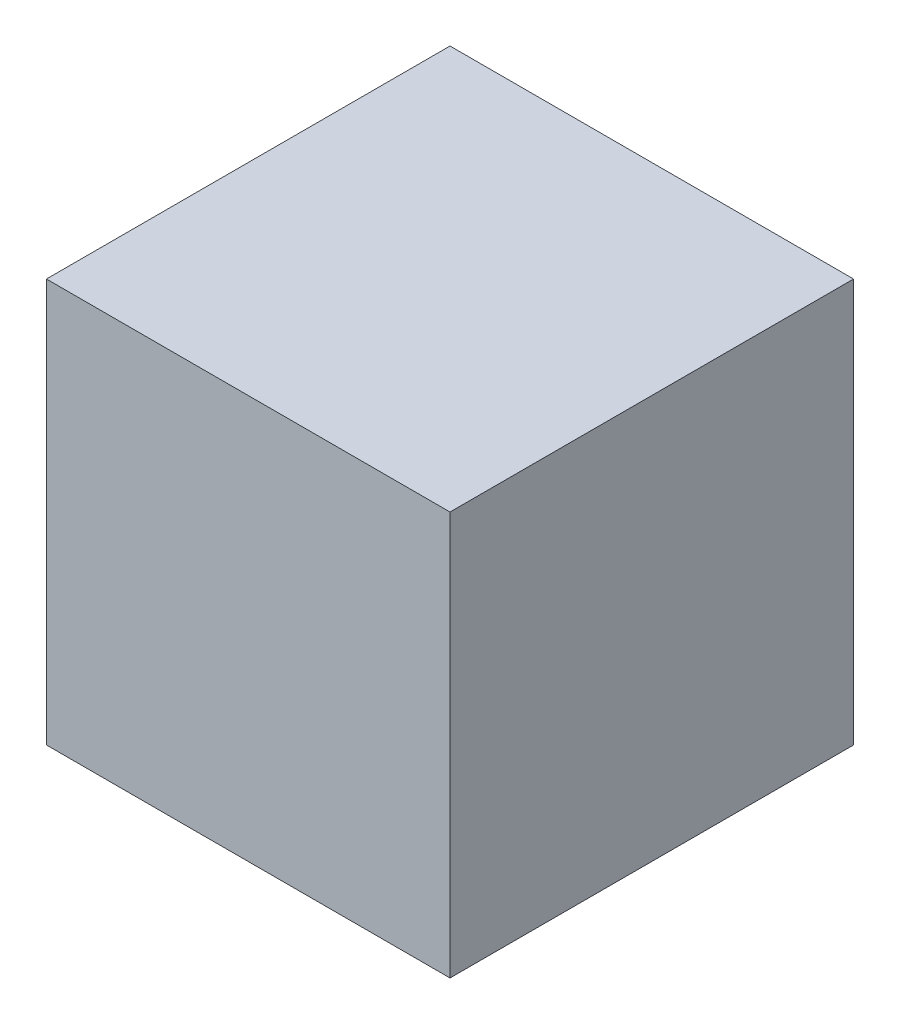
SolidWorks part; units mm, degrees
ref_plane "Front Plane" through (0, 0, 0) normal (0, 0, 1) x (1, 0, 0)
ref_plane "Top Plane" through (0, 0, 0) normal (0, 1, 0) x (1, 0, 0)
ref_plane "Right Plane" through (0, 0, 0) normal (1, 0, 0) x (0, 0, -1)
sketch "Sketch1" plane through (0, 0, 0) normal (0, 0, 1) x (1, 0, 0)
  line L0 (-28.5, 28.5) -> (28.5, -28.5) construction
  line L1 (-28.5, 28.5) -> (28.5, 28.5)
  line L2 (-28.5, 28.5) -> (-28.5, -28.5)
  line L3 (-28.5, -28.5) -> (28.5, -28.5)
  line L4 (28.5, 28.5) -> (28.5, -28.5)
  line L5 (28.5, 28.5) -> (0, 0) construction
  line L6 (0, 0) -> (-28.5, -28.5) construction
  dimension "D1" = 57
extrude "Boss-Extrude1" add sketch "Sketch1" along normal blind 57
